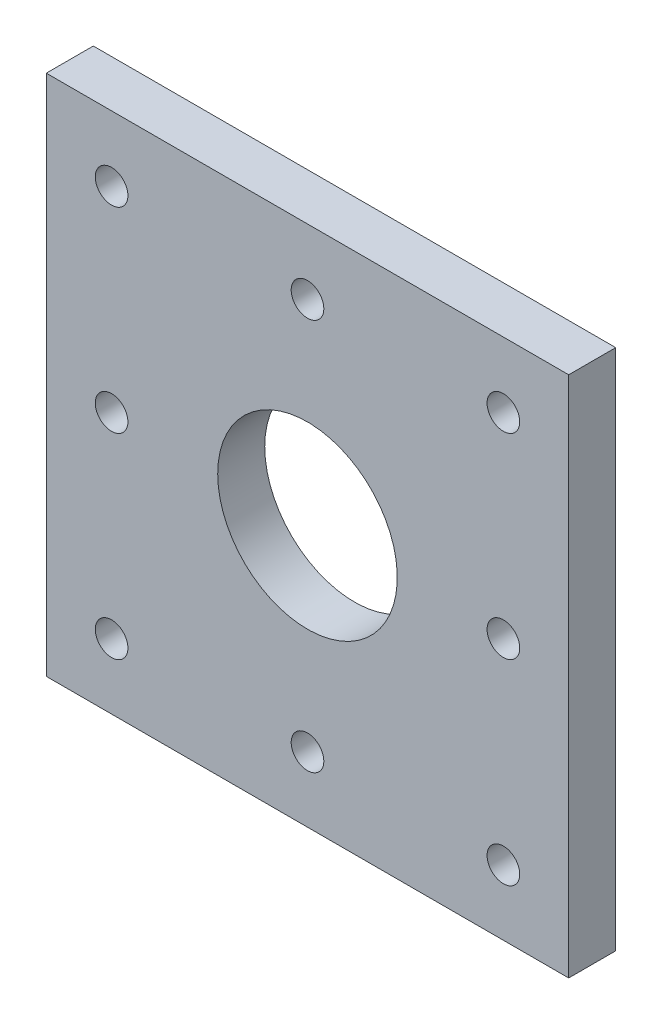
SolidWorks part; units mm, degrees
ref_plane "Front Plane" through (0, 0, 0) normal (0, 0, 1) x (1, 0, 0)
ref_plane "Top Plane" through (0, 0, 0) normal (0, 1, 0) x (1, 0, 0)
ref_plane "Right Plane" through (0, 0, 0) normal (1, 0, 0) x (0, 0, -1)
sketch "Sketch1" plane through (0, 0, 0) normal (0, 0, 1) x (1, 0, 0)
  line L1 (0, 0) -> (50.8, 0)
  line L2 (0, 0) -> (0, 50.8)
  line L3 (0, 50.8) -> (50.8, 50.8)
  line L4 (50.8, 0) -> (50.8, 50.8)
  dimension "D1" = 50.8
  dimension "D2" = 50.8
extrude "Boss-Extrude1" add sketch "Sketch1" along normal blind 4.572
sketch "Sketch2" plane through (0, 0, 0) normal (0, 0, -1) x (-1, 0, 0)
  line L0 (0, 25.4) -> (-50.8, 25.4) construction
  line L1 (0, 50.8) -> (0, 0) construction
  line L2 (-50.8, 0) -> (-50.8, 50.8) construction
  line L3 (-25.4, 50.8) -> (-25.4, 0) construction
  line L4 (-50.8, 50.8) -> (0, 50.8) construction
  line L5 (0, 0) -> (-50.8, 0) construction
  circle A0 centre (-25.4, 25.4) radius 8.7313
  dimension "D1" = 17.4625
sketch "Sketch4" plane through (0, 0, 0) normal (0, 0, -1) x (-1, 0, 0)
  line L0 (-25.4, 50.8) -> (-25.4, 0) construction
  line L1 (-50.8, 50.8) -> (0, 50.8) construction
  line L2 (0, 0) -> (-50.8, 0) construction
  line L3 (-50.8, 25.4) -> (0, 25.4) construction
  line L4 (-50.8, 0) -> (-50.8, 50.8) construction
  line L5 (0, 50.8) -> (0, 0) construction
ref_plane "Plane1" through (25.4, 0, 0) normal (1, 0, 0) x (0, -1, 0)
ref_plane "Plane2" through (0, 25.4, 0) normal (0, -1, 0) x (-1, 0, 0)
extrude "Cut-Extrude7" cut sketch "Sketch2" against normal through all contours A0
sketch "Sketch5" plane through (0, 0, 4.572) normal (0, 0, 1) x (1, 0, 0)
  line L0 (25.4, 0) -> (25.4, 6.35) construction
  line L1 (0, 0) -> (50.8, 0) construction
  line L2 (50.8, 25.4) -> (44.45, 25.4) construction
  line L3 (50.8, 0) -> (50.8, 50.8) construction
  line L4 (25.4, 50.8) -> (25.4, 44.45) construction
  line L5 (50.8, 50.8) -> (0, 50.8) construction
  line L6 (0, 25.4) -> (6.35, 25.4) construction
  line L7 (0, 50.8) -> (0, 0) construction
  circle A0 centre (25.4, 6.35) radius 1.5875
  circle A1 centre (6.35, 25.4) radius 1.5875
  circle A2 centre (25.4, 44.45) radius 1.5875
  circle A3 centre (44.45, 25.4) radius 1.5875
  dimension "D1" = 3.175
  dimension "D4" = 3.175
  dimension "D6" = 3.175
  dimension "D7" = 3.175
  dimension "D2" = 6.35
  dimension "D3" = 6.35
  dimension "D5" = 6.35
  dimension "D8" = 6.35
extrude "Cut-Extrude8" cut sketch "Sketch5" against normal through all
sketch "Sketch7" plane through (0, 0, 0) normal (0, 0, -1) x (-1, 0, 0)
  circle A0 centre (-6.35, 6.35) radius 1.5875
  circle A1 centre (-44.45, 6.35) radius 1.5875
  circle A2 centre (-44.45, 44.45) radius 1.5875
  circle A3 centre (-6.35, 44.45) radius 1.5875
  dimension "D1" = 3.175
  dimension "D2" = 3.175
  dimension "D3" = 3.175
  dimension "D4" = 3.175
extrude "Cut-Extrude9" cut sketch "Sketch7" against normal through all
equation "\"dist\"= 10"
